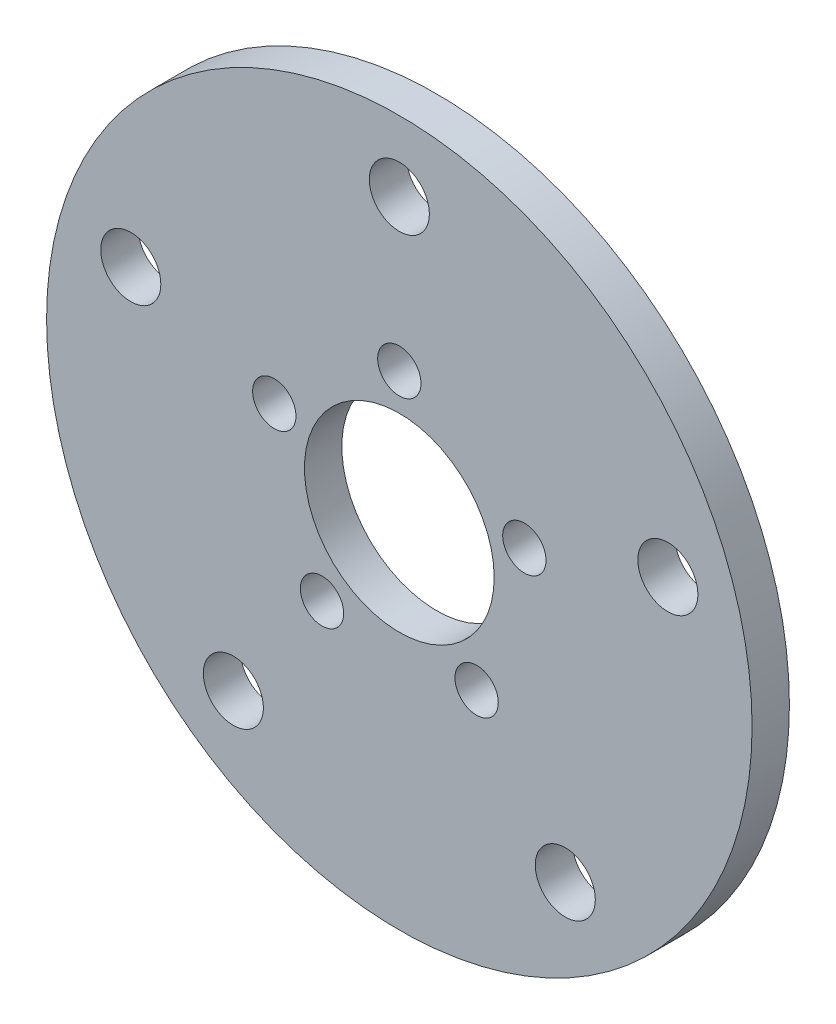
SolidWorks part; units mm, degrees
ref_plane "Front Plane" through (0, 0, 0) normal (0, 0, 1) x (1, 0, 0)
ref_plane "Top Plane" through (0, 0, 0) normal (0, 1, 0) x (1, 0, 0)
ref_plane "Right Plane" through (0, 0, 0) normal (1, 0, 0) x (0, 0, -1)
sketch "Sketch1" plane through (0, 0, 0) normal (0, 0, 1) x (1, 0, 0)
  line L0 (0, 0) -> (0, 11.176) construction
  line L1 (0, 24) -> (0, 0) construction
  circle A0 centre (0, 0) radius 29.9847
  circle A1 centre (0, 0) radius 8.0645
  circle A2 centre (0, 11.176) radius 1.8415
  circle A3 centre (0, 24) radius 2.5527
  circle A4 centre (10.629, 3.4536) radius 1.8415
  circle A5 centre (22.8254, 7.4164) radius 2.5527
  circle A6 centre (6.5691, -9.0416) radius 1.8415
  circle A7 centre (14.1068, -19.4164) radius 2.5527
  circle A8 centre (-6.5691, -9.0416) radius 1.8415
  circle A9 centre (-14.1068, -19.4164) radius 2.5527
  circle A10 centre (-10.629, 3.4536) radius 1.8415
  circle A11 centre (-22.8254, 7.4164) radius 2.5527
  circle A12 centre (0, 0) radius 29.9847 construction
  dimension "D2" = 16.129
  dimension "D4" = 3.683
  dimension "D5" = 5.1054
  dimension "D3" = 11.176
  dimension "D6" = 24
  dimension "D7" = 5
extrude "Boss-Extrude1" add sketch "Sketch1" along normal blind 3.175 contours A0
